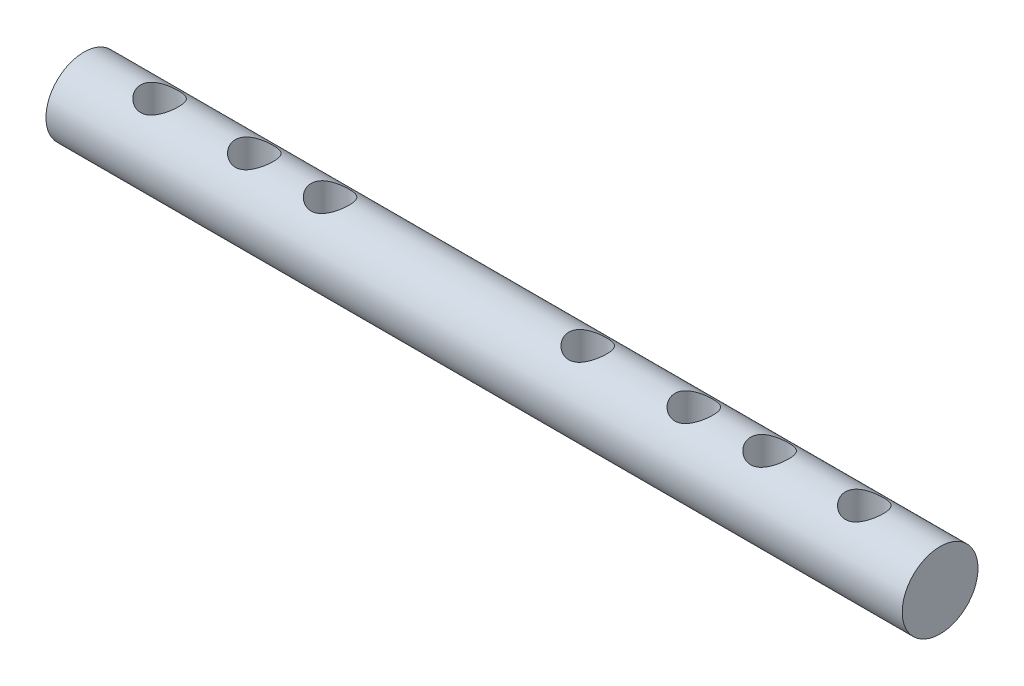
SolidWorks part; units mm, degrees
material "3003 Alloy"
ref_plane "Front Plane" through (0, 0, 0) normal (0, 0, 1) x (1, 0, 0)
ref_plane "Top Plane" through (0, 0, 0) normal (0, 1, 0) x (1, 0, 0)
ref_plane "Right Plane" through (0, 0, 0) normal (1, 0, 0) x (0, 0, -1)
sketch "Sketch1" plane through (0, 0, 0) normal (1, 0, 0) x (0, 0, -1)
  circle A0 centre (0, 0) radius 10
extrude "Boss-Extrude1" add sketch "Sketch1" along normal blind 226
sketch "Sketch2" plane through (0, 0, 0) normal (0, 1, 0) x (1, 0, 0)
  circle A0 centre (20, 0) radius 5
  circle A1 centre (206, 0) radius 5
  circle A2 centre (181, 0) radius 5
  circle A3 centre (45, 0) radius 5
  circle A4 centre (161, 0) radius 5
  circle A5 centre (65, 0) radius 5
  circle A6 centre (133, 0) radius 5
extrude "Cut-Extrude1" cut sketch "Sketch2" against normal through all and the other way through all
